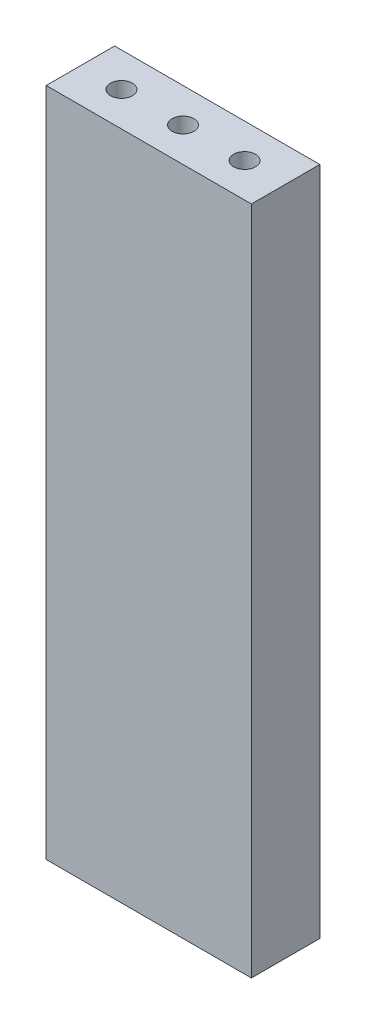
SolidWorks part; units mm, degrees
ref_plane "Front Plane" through (0, 0, 0) normal (0, 0, 1) x (1, 0, 0)
ref_plane "Top Plane" through (0, 0, 0) normal (0, 1, 0) x (1, 0, 0)
ref_plane "Right Plane" through (0, 0, 0) normal (1, 0, 0) x (0, 0, -1)
sketch "Sketch1" plane through (0, 0, 0) normal (0, 1, 0) x (1, 0, 0)
  line L1 (-7.5, -2.5) -> (7.5, -2.5)
  line L2 (-7.5, -2.5) -> (-7.5, 2.5)
  line L3 (-7.5, 2.5) -> (7.5, 2.5)
  line L4 (7.5, -2.5) -> (7.5, 2.5)
  line L5 (-7.5, -2.5) -> (7.5, 2.5) construction
  line L6 (-7.5, 2.5) -> (7.5, -2.5) construction
  point P0 (0, 0)
  dimension "D1" = 15
  dimension "D2" = 5
extrude "Boss-Extrude1" add sketch "Sketch1" against normal blind 49
hole_wizard "M2 Tapped Hole1" positions "Sketch3" profile "Sketch2" tap size "M2" standard "ISO"
sketch "Sketch3" plane through (0, -49, 0) normal (0, -1, 0) x (1, 0, 0)
  line L0 (-7.5, 0) -> (7.5, 0) construction
  line L1 (-7.5, -2.5) -> (-7.5, 2.5) construction
  line L2 (7.5, 2.5) -> (7.5, -2.5) construction
  point P0 (-4.5, 0)
  point P1 (4.5, 0)
  point P12 (0, 0)
  dimension "D1" = 3
  dimension "D2" = 3
sketch "Sketch2" plane through (-4.5, -49, 0) normal (1, 0, 0) x (0, 0, -1)
  line L0 (0, 0) -> (0, 11.6807)
  line L1 (0, 11.6807) -> (0.8, 11.2)
  line L2 (0.8, 11.2) -> (0.8, 0)
  line L5 (0.8, 0) -> (0, 0)
  line L10 (0, 11.6807) -> (-0.8, 11.2) construction
  line L11 (0, -6.35) -> (0, 107.95) construction
  dimension "Tap Drill Dia." = 1.6
  dimension "Tap Drill Depth" = 11.2
  dimension "Drill Angle" = 118
cosmetic thread "Hole Thread1"
cosmetic thread "Hole Thread2"
cosmetic thread "Hole Thread3"
hole_wizard "M2 Tapped Hole2" positions "Sketch5" profile "Sketch4" tap size "M2" standard "ISO"
sketch "Sketch5" plane through (0, 0, 0) normal (0, 1, 0) x (-1, 0, 0)
  point P0 (4.5, 0)
  point P1 (0, 0)
  point P3 (-4.5, 0)
  dimension "D1" = 4.5
  dimension "D2" = 4.5
sketch "Sketch4" plane through (-4.5, 0, 0) normal (1, 0, 0) x (0, 0, 1)
  line L0 (0, 0) -> (0, 11.6807)
  line L1 (0, 11.6807) -> (0.8, 11.2)
  line L2 (0.8, 11.2) -> (0.8, 0)
  line L5 (0.8, 0) -> (0, 0)
  line L10 (0, 11.6807) -> (-0.8, 11.2) construction
  line L11 (0, -6.35) -> (0, 107.95) construction
  dimension "Tap Drill Dia." = 1.6
  dimension "Tap Drill Depth" = 11.2
  dimension "Drill Angle" = 118
cosmetic thread "Hole Thread4"
cosmetic thread "Hole Thread5"
cosmetic thread "Hole Thread6"
equation "\"D2@Sketch5\" = \"D1@Sketch5\""
